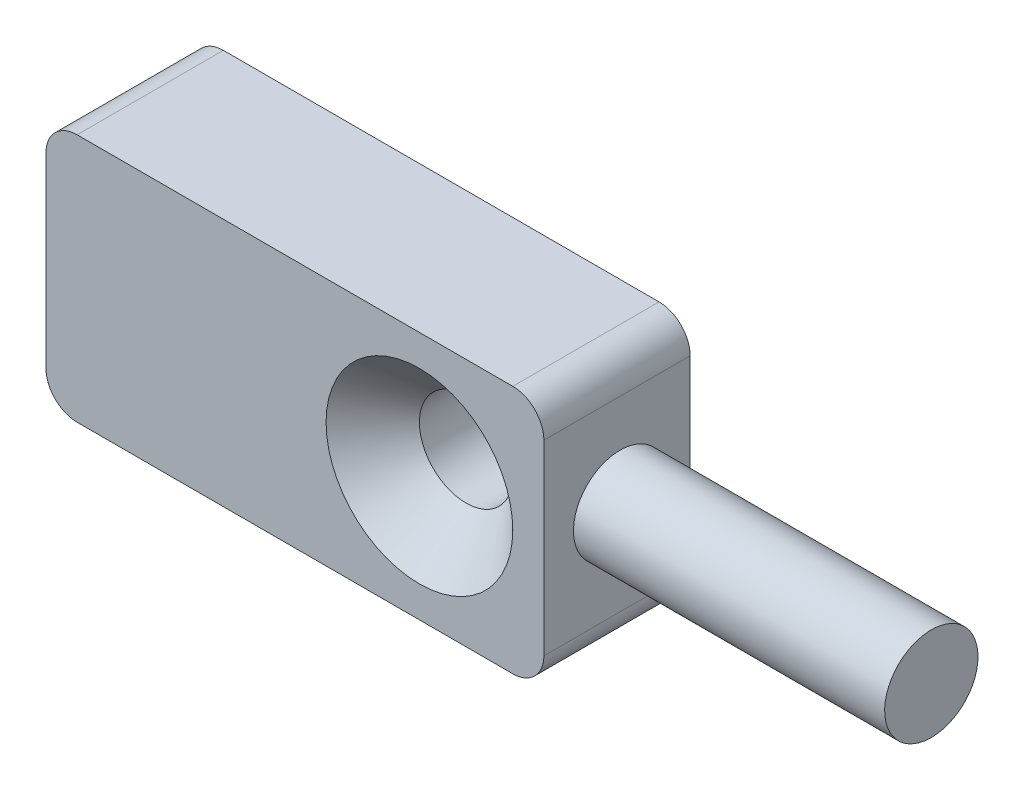
SolidWorks part; units mm, degrees
ref_plane "Vorne" through (0, 0, 0) normal (0, 0, 1) x (1, 0, 0)
ref_plane "Oben" through (0, 0, 0) normal (0, 1, 0) x (1, 0, 0)
ref_plane "Rechts" through (0, 0, 0) normal (1, 0, 0) x (0, 0, -1)
sketch "Skizze1" plane through (0, 0, 0) normal (0, 0, 1) x (1, 0, 0)
  line L0 (0, -55) -> (0, 55) construction
  line L1 (0, 4) -> (-16, 4)
  line L2 (0, 4) -> (0, -4)
  line L3 (0, -4) -> (-16, -4)
  line L4 (-16, 4) -> (-16, -4)
  line L5 (55, 0) -> (-55, 0) construction
  circle A0 centre (-4, 0) radius 1.5
  dimension "D4" = 3
  dimension "D1" = 16
  dimension "D2" = 8
  dimension "D3" = 4
  dimension "D5" = 4
extrude "Aufsatz-Linear austragen1" add sketch "Skizze1" along normal blind 4.7
fillet "Verrundung1" radius 1 4 edges at (0, -4, 2.35) (-16, -4, 2.35) (0, 4, 2.35) (-16, 4, 2.35)
chamfer "Fase1" distance 1.5 angle 45 1 edges at (-2.5, 0, 4.7)
sketch "Skizze2" plane through (0, 0, 0) normal (1, 0, 0) x (0, 0, -1)
  line L0 (0, -3) -> (0, 3) construction
  circle A0 centre (-2.25, 0) radius 1.5
  dimension "D1" = 3
  dimension "D2" = 2.25
extrude "Aufsatz-Linear austragen2" add sketch "Skizze2" along normal blind 10
